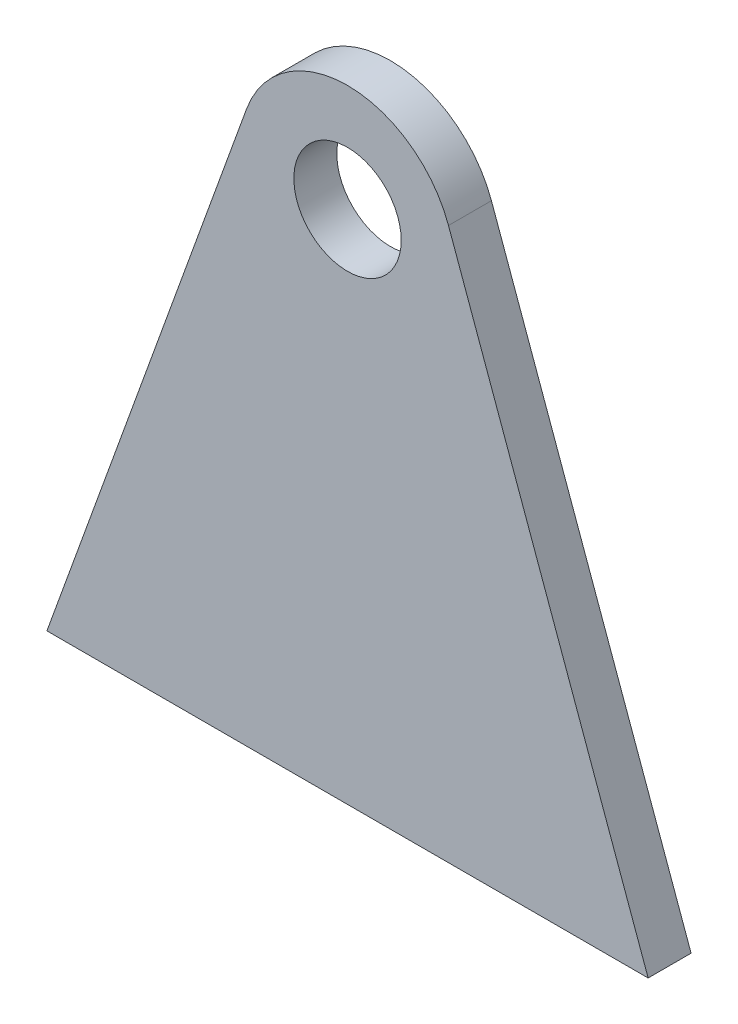
SolidWorks part; units mm, degrees
ref_plane "Front Plane" through (0, 0, 0) normal (0, 0, 1) x (1, 0, 0)
ref_plane "Top Plane" through (0, 0, 0) normal (0, 1, 0) x (1, 0, 0)
ref_plane "Right Plane" through (0, 0, 0) normal (1, 0, 0) x (0, 0, -1)
sketch "Sketch1" plane through (0, 0, 0) normal (0, 0, 1) x (1, 0, 0)
  line L1 (-140, -240) -> (140, -240)
  line L2 (-140, -240) -> (-47.0176, 17.0102)
  line L3 (140, -240) -> (47.0176, 17.0102)
  circle A0 centre (0, 0) radius 25
  arc A1 (47.0176, 17.0102) -> (-47.0176, 17.0102) centre (0, 0) ccw
  point P10 (0, -240)
  dimension "D1" = 280
  dimension "D3" = 100
  dimension "D4" = 50
  dimension "D2" = 240
extrude "Boss-Extrude1" add sketch "Sketch1" along normal mid plane 20
